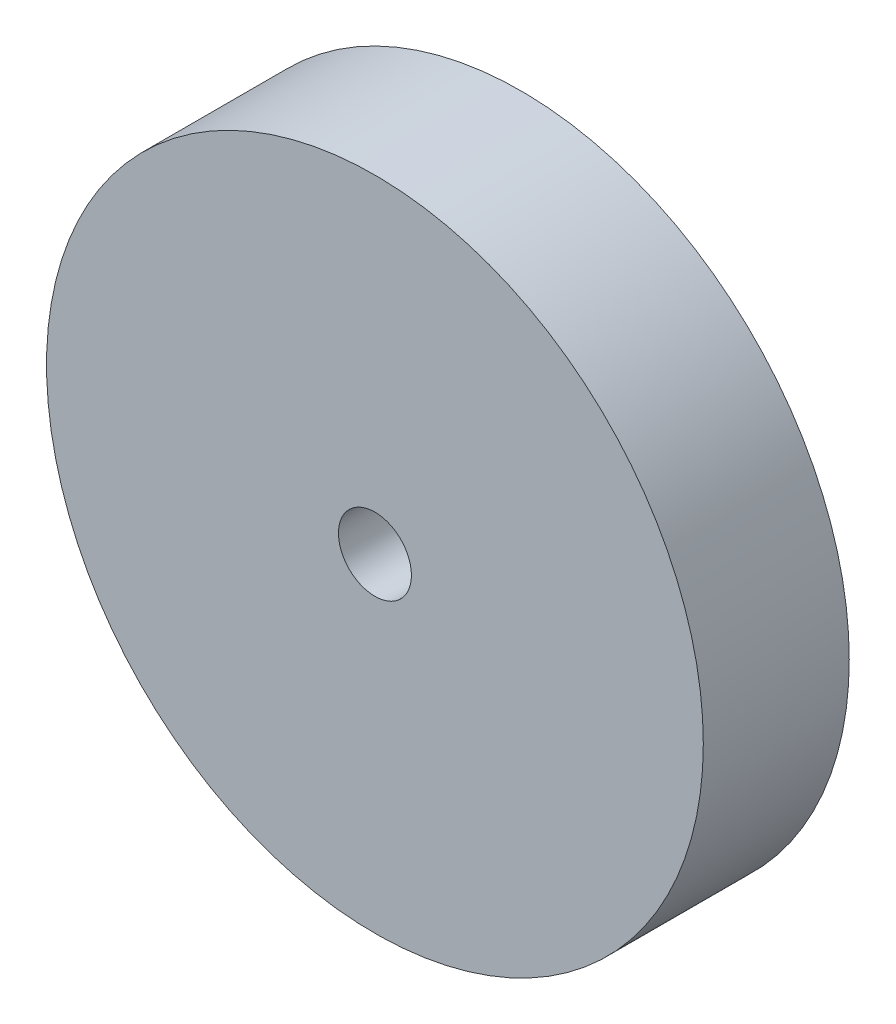
SolidWorks part; units mm, degrees
material "ABS"
ref_plane "前视基准面" through (0, 0, 0) normal (0, 0, 1) x (1, 0, 0)
ref_plane "上视基准面" through (0, 0, 0) normal (0, 1, 0) x (1, 0, 0)
ref_plane "右视基准面" through (0, 0, 0) normal (1, 0, 0) x (0, 0, -1)
other "Configuration Table"
sketch "草图1" plane through (0, 0, 0) normal (0, 0, 1) x (1, 0, 0)
  circle A0 centre (0, 0) radius 9
  dimension "D1" = 18
extrude "凸台-拉伸1" add sketch "草图1" along normal blind 4
sketch "草图2" plane through (0, 0, 4) normal (0, 0, 1) x (1, 0, 0)
  circle A0 centre (0, 0) radius 1
  dimension "D1" = 2
extrude "切除-拉伸1" cut sketch "草图2" against normal through all
